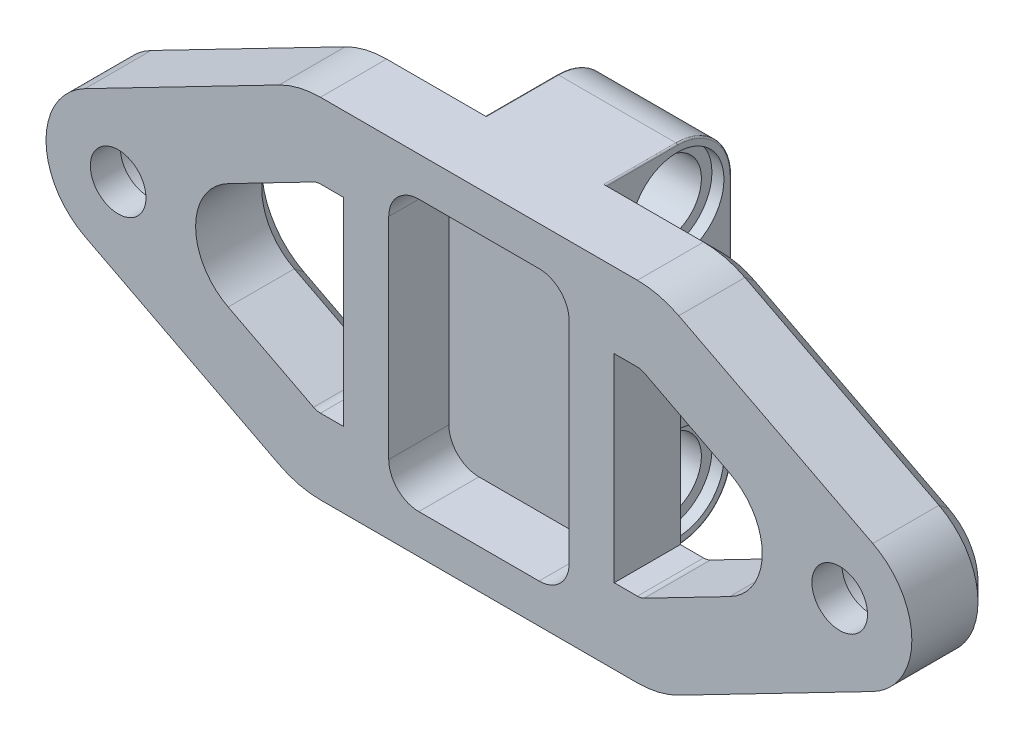
SolidWorks part; units mm, degrees
ref_plane "正面" through (0, 0, 0) normal (0, 0, 1) x (1, 0, 0)
ref_plane "平面" through (0, 0, 0) normal (0, 1, 0) x (1, 0, 0)
ref_plane "右側面" through (0, 0, 0) normal (1, 0, 0) x (0, 0, -1)
sketch "ｽｹｯﾁ2" plane through (0, 0, 0) normal (0, 0, 1) x (1, 0, 0)
  line L0 (-4, 11.6) -> (-12, 11.6) construction
  line L1 (4, -11.6) -> (-4, -11.6) construction
  line L2 (4, -11.6) -> (4, 11.6) construction
  line L3 (4, 11.6) -> (-4, 11.6) construction
  line L4 (-4, -11.6) -> (-4, 11.6) construction
  line L5 (4, -11.6) -> (-4, 11.6) construction
  line L6 (4, 11.6) -> (-4, -11.6) construction
  line L7 (-12, 11.6) -> (-12, -11.6) construction
  line L8 (-12, -11.6) -> (-4, -11.6) construction
  line L9 (4, 11.6) -> (12, 11.6) construction
  line L10 (12, 11.6) -> (12, -11.6) construction
  line L11 (12, -11.6) -> (4, -11.6) construction
  line L12 (-12, 11.6) -> (-26.2026, 4.2648)
  line L13 (-26.2026, -4.2648) -> (-12, -11.6)
  line L14 (26.2026, 4.2648) -> (12, 11.6)
  line L15 (26.2026, -4.2648) -> (12, -11.6)
  line L16 (-12, 11.6) -> (12, 11.6)
  line L17 (12, -11.6) -> (-12, -11.6)
  arc A0 (-26.2026, 4.2648) -> (-26.2026, -4.2648) centre (-24, 0) ccw
  arc A1 (26.2026, 4.2648) -> (26.2026, -4.2648) centre (24, 0) cw
  circle A2 centre (-24, 0) radius 1.85
  circle A3 centre (24, 0) radius 1.85
  circle A4 centre (-24, 0) radius 2.95 construction
  circle A5 centre (24, 0) radius 2.95 construction
  point P0 (0, 0)
  dimension "D4" = 4.8
  dimension "D5" = 3.7
  dimension "D6" = 5.9
  dimension "D1" = 8
  dimension "D2" = 23.2
  dimension "D3" = 48
extrude "ﾎﾞｽ - 押し出し1" add sketch "ｽｹｯﾁ2" along normal blind 5.6
sketch "ｽｹｯﾁ3" plane through (0, 0, 0) normal (0, 0, -1) x (-1, 0, 0)
  circle A0 centre (-24, 0) radius 2.95
  circle A1 centre (24, 0) radius 2.95
  circle A2 centre (-24, 0) radius 2.95 construction
extrude "ｶｯﾄ - 押し出し1" cut sketch "ｽｹｯﾁ3" against normal blind 3.6
sketch "ｽｹｯﾁ4" plane through (0, 0, 0) normal (0, 0, -1) x (-1, 0, 0)
  line L1 (-4, 11.6) -> (4, 11.6)
  line L2 (-4, 11.6) -> (-4, -11.6)
  line L3 (-4, -11.6) -> (4, -11.6)
  line L4 (4, 11.6) -> (4, -11.6)
  line L5 (-4, 11.6) -> (4, -11.6) construction
  line L6 (-4, -11.6) -> (4, 11.6) construction
  point P4 (0, 0)
  point P7 (4, -11)
extrude "ﾎﾞｽ - 押し出し2" add sketch "ｽｹｯﾁ4" along normal blind 7.2
sketch "ｽｹｯﾁ5" plane through (4, 0, 0) normal (1, 0, 0) x (0, 0, -1)
  line L0 (3.6, 8) -> (3.6, -8) construction
  line L1 (0, 4.2648) -> (0, -4.2648) construction
  line L2 (7.2, 11.6) -> (7.2, -11.6) construction
  line L3 (2.8, 2.2627) -> (2.8, 0.8)
  line L4 (2.8, 0.8) -> (1.3373, 0.8)
  line L5 (3.6, 0) -> (50003.6, 0) construction
  line L6 (7.2, 11.6) -> (0, 11.6) construction
  line L7 (7.2, -11.6) -> (0, -11.6) construction
  line L8 (4.4, 2.2627) -> (4.4, 0.8)
  line L9 (1.3373, 0.8) -> (5.8627, 0.8) construction
  line L10 (1.3373, 0.8) -> (1.3373, -0.8) construction
  line L11 (1.3373, -0.8) -> (5.8627, -0.8) construction
  line L12 (5.8627, 0.8) -> (5.8627, -0.8) construction
  line L13 (1.3373, 0.8) -> (5.8627, -0.8) construction
  line L14 (1.3373, -0.8) -> (5.8627, 0.8) construction
  line L15 (2.8, 2.2627) -> (4.4, 2.2627) construction
  line L16 (2.8, 2.2627) -> (2.8, -2.2627) construction
  line L17 (2.8, -2.2627) -> (4.4, -2.2627) construction
  line L18 (4.4, 2.2627) -> (4.4, -2.2627) construction
  line L19 (2.8, 2.2627) -> (4.4, -2.2627) construction
  line L20 (2.8, -2.2627) -> (4.4, 2.2627) construction
  line L21 (4.4, 0.8) -> (5.8627, 0.8)
  line L22 (5.8627, -0.8) -> (4.4, -0.8)
  line L23 (4.4, -0.8) -> (4.4, -2.2627)
  line L24 (1.3373, -0.8) -> (2.8, -0.8)
  line L25 (2.8, -0.8) -> (2.8, -2.2627)
  circle A0 centre (3.6, 8) radius 2.4
  circle A1 centre (3.6, -8) radius 2.4
  circle A2 centre (3.6, 0) radius 2.4 construction
  arc A3 (1.3373, 0.8) -> (1.3373, -0.8) centre (3.6, 0) ccw
  arc A4 (2.8, 2.2627) -> (4.4, 2.2627) centre (3.6, 0) cw
  arc A5 (5.8627, -0.8) -> (5.8627, 0.8) centre (3.6, 0) ccw
  arc A6 (2.8, -2.2627) -> (4.4, -2.2627) centre (3.6, 0) ccw
  point P8 (3.6, 0)
  point P21 (3.6, 0)
  point P26 (3.6, 0)
  point P33 (0, 0)
  dimension "D1" = 4.8
  dimension "D2" = 16
  dimension "D3" = 1.6
extrude "ｶｯﾄ - 押し出し2" cut sketch "ｽｹｯﾁ5" against normal through all
fillet "ﾌｨﾚｯﾄ1" radius 3.6 2 edges at (0, -11.6, -7.2) (0, 11.6, -7.2)
sketch "ｽｹｯﾁ6" plane through (4, 0, 0) normal (1, 0, 0) x (0, 0, -1)
  circle A0 centre (3.6, 8) radius 3.1
  circle A1 centre (3.6, -8) radius 3.1
  dimension "D1" = 6.2
  dimension "D2" = 6.2
extrude "ｶｯﾄ - 押し出し3" cut sketch "ｽｹｯﾁ6" against normal blind 0.8
ref_plane "平面1" through (0, 0, 0) normal (1, 0, 0) x (0, 0, -1)
mirror "ﾐﾗｰ1" about plane through (0, 0, 0) normal (1, 0, 0) of "ｶｯﾄ - 押し出し3"
fillet "ﾌｨﾚｯﾄ2" radius 6 4 edges at (-12, -11.6, 2.8) (12, -11.6, 2.8) (-12, 11.6, 2.8) (12, 11.6, 2.8)
sketch "ｽｹｯﾁ7" plane through (0, 0, 0) normal (0, 0, -1) x (-1, 0, 0)
  line L22 (-23.5642, 0) -> (-11.001, -6.4885)
  line L23 (-10.5421, -6.6) -> (-9, -6.6)
  line L24 (-9, -6.6) -> (-9, 6.6)
  line L25 (-9, 6.6) -> (-10.5421, 6.6)
  line L26 (-11.001, 6.4885) -> (-23.5642, 0)
  line L27 (-16.6828, -3.554) -> (-11.001, -6.4885)
  line L28 (-10.5421, -6.6) -> (-9, -6.6)
  line L29 (-9, -6.6) -> (-9, 6.6)
  line L30 (-9, 6.6) -> (-10.5421, 6.6)
  line L31 (-11.001, 6.4885) -> (-16.6828, 3.554)
  arc A3 (-16.6828, 3.554) -> (-16.6828, -3.554) centre (-14.8473, 0) ccw
  arc A6 (-11.001, -6.4885) -> (-10.5421, -6.6) centre (-10.5421, -5.6) ccw
  arc A7 (-10.5421, 6.6) -> (-11.001, 6.4885) centre (-10.5421, 5.6) ccw
  arc A8 (-11.001, -6.4885) -> (-10.5421, -6.6) centre (-10.5421, -5.6) ccw
  arc A9 (-10.5421, 6.6) -> (-11.001, 6.4885) centre (-10.5421, 5.6) ccw
  point P3 (0, 0)
  point P4 (0, 0)
  point P5 (-19.0563, -2.3282)
  dimension "D2" = 4
  dimension "D1" = 5
extrude "ｶｯﾄ - 押し出し4" cut sketch "ｽｹｯﾁ7" against normal through all
mirror "ﾐﾗｰ2" about plane through (0, 0, 0) normal (1, 0, 0) of "ｶｯﾄ - 押し出し4"
chamfer "面取り1" distance 1.2 angle 45 30 edges at (-7.271, 11.6, 0) (-11.9588, 11.4303, 0) (-19.749, 7.5979, 0) (-28.8, 0, 0) (-19.749, -7.5979, 0) (-11.9588, -11.4303, 0) (-7.271, -11.6, 0) (7.271, -11.6, 0) (11.9588, -11.4303, 0) (19.749, -7.5979, 0) (28.8, 0, 0) (19.749, 7.5979, 0) (11.9588, 11.4303, 0) (7.271, 11.6, 0) (-9, 0, 0) (-9.771, 6.6, 0) (-9.771, -6.6, 0) (-10.7782, 6.5717, 0) (-10.7782, -6.5717, 0) (-13.8419, 5.0212, 0) (-13.8419, -5.0212, 0) (-18.8473, 0, 0) (9, 0, 0) (9.771, -6.6, 0) (10.7782, -6.5717, 0) (9.771, 6.6, 0) (13.8419, -5.0212, 0) (10.7782, 6.5717, 0) (18.8473, 0, 0) (13.8419, 5.0212, 0)
sketch "ｽｹｯﾁ8" plane through (0, 0, 5.6) normal (0, 0, 1) x (1, 0, 0)
  line L1 (-6, 9) -> (6, 9)
  line L2 (-6, 9) -> (-6, -9)
  line L3 (-6, -9) -> (6, -9)
  line L4 (6, 9) -> (6, -9)
  line L5 (-6, 9) -> (6, -9) construction
  line L6 (-6, -9) -> (6, 9) construction
  point P4 (0, 0)
  point P5 (0, 0)
  point P6 (5.4607, -3.4685)
  point P7 (6, -9.3613)
  point P8 (0, 0)
  dimension "D1" = 18
  dimension "D2" = 12
extrude "ｶｯﾄ - 押し出し5" cut sketch "ｽｹｯﾁ8" against normal blind 4
fillet "ﾌｨﾚｯﾄ3" radius 2 4 edges at (6, -9, 3.6) (6, 9, 3.6) (-6, -9, 3.6) (-6, 9, 3.6)
fillet "ﾌｨﾚｯﾄ4" radius 0.1 10 edges at (-4, -11.6, -1.2) (-4, -10.5456, -6.1456) (-4, 11.6, -1.2) (-4, 10.5456, -6.1456) (4, 11.6, -1.2) (4, 10.5456, -6.1456) (4, -11.6, -1.2) (4, -10.5456, -6.1456) (-4, 0, -7.2) (4, 0, -7.2)
sketch "ｽｹｯﾁ9" plane through (4, 0, 0) normal (1, 0, 0) x (0, 0, -1)
  line L0 (4.4, -0.8) -> (5.8627, -0.8) construction
  line L1 (4.4, 0.8) -> (4.5, 0.8)
  line L2 (4.4, 0.8) -> (4.4, -0.8)
  line L3 (4.4, -0.8) -> (4.5, -0.8)
  line L4 (4.5, 0.8) -> (4.5, -0.8)
  line L5 (4.4, 0.8) -> (4.5, -0.8) construction
  line L6 (4.4, -0.8) -> (4.5, 0.8) construction
  point P4 (4.45, 0)
  dimension "D1" = 0.1
extrude "ﾎﾞｽ - 押し出し3" add sketch "ｽｹｯﾁ9" against normal up to surface (8 mm away) separate body up to face at (-4, 8, -6.7)
